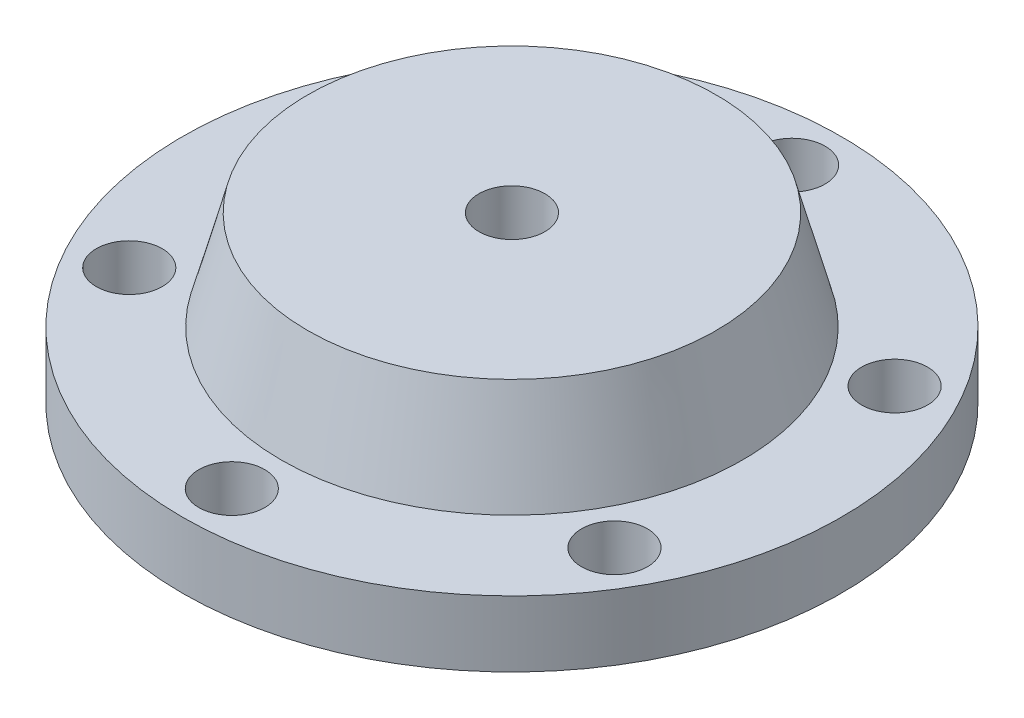
SolidWorks part; units mm, degrees
material "6061-T6 (SS)"
ref_plane "Front Plane" through (0, 0, 0) normal (0, 0, 1) x (1, 0, 0)
ref_plane "Top Plane" through (0, 0, 0) normal (0, 1, 0) x (1, 0, 0)
ref_plane "Right Plane" through (0, 0, 0) normal (1, 0, 0) x (0, 0, -1)
sketch "Sketch2" plane through (0, 0, 0) normal (0, 1, 0) x (1, 0, 0)
  circle A0 centre (0, 0) radius 254
  circle A1 centre (0, 215.9) radius 25.4
  circle A2 centre (186.9749, 107.95) radius 25.4
  circle A3 centre (186.9749, -107.95) radius 25.4
  circle A4 centre (0, -215.9) radius 25.4
  circle A5 centre (-186.9749, -107.95) radius 25.4
  circle A6 centre (-186.9749, 107.95) radius 25.4
  point P17 (0, 0)
  dimension "D1" = 508
  dimension "D2" = 6
extrude "Boss-Extrude2" add sketch "Sketch2" along normal blind 50.8
sketch "Sketch3" plane through (0, 50.8, 0) normal (0, 1, 0) x (1, 0, 0)
  circle A0 centre (0, 0) radius 177.8
  dimension "D1" = 355.6
extrude "Boss-Extrude3" add sketch "Sketch3" along normal blind 76.2 draft 15
sketch "Sketch4" plane through (0, 127, 0) normal (0, 1, 0) x (1, 0, 0)
  circle A0 centre (0, 0) radius 25.4
  dimension "D1" = 50.8
extrude "Cut-Extrude1" cut sketch "Sketch4" against normal blind 76.2
